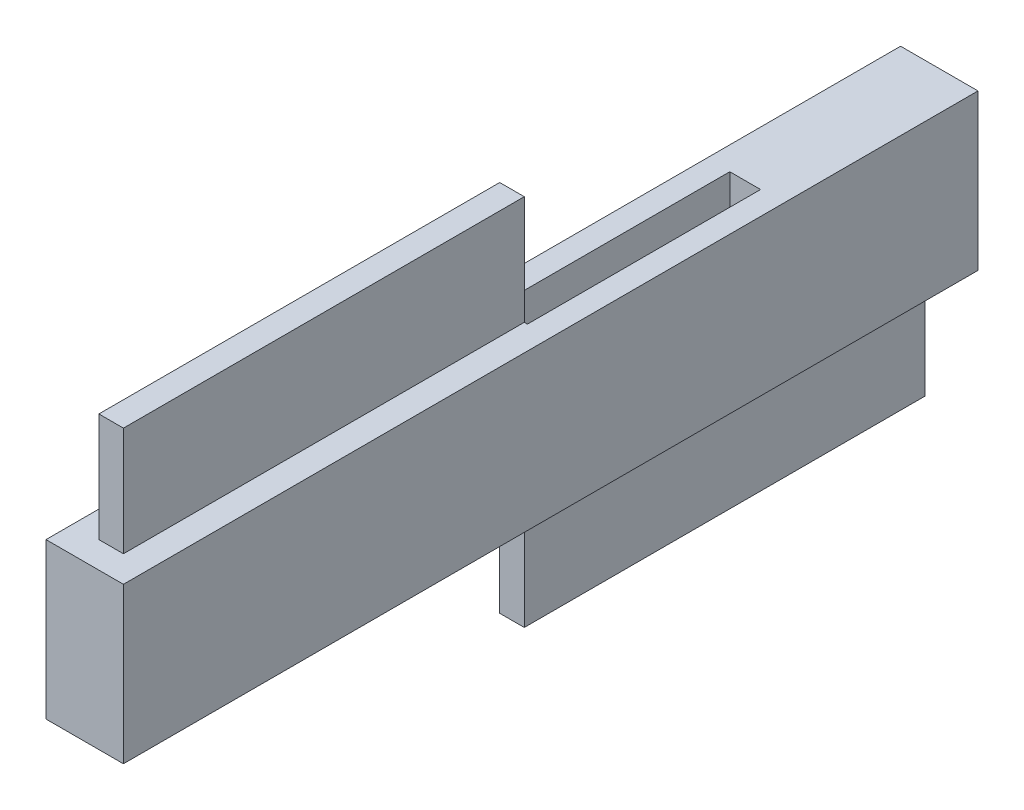
SolidWorks part; units mm, degrees
ref_plane "Front Plane" through (0, 0, 0) normal (0, 0, 1) x (1, 0, 0)
ref_plane "Top Plane" through (0, 0, 0) normal (0, 1, 0) x (1, 0, 0)
ref_plane "Right Plane" through (0, 0, 0) normal (1, 0, 0) x (0, 0, -1)
sketch "Sketch1" plane through (0, 0, 0) normal (0, 1, 0) x (1, 0, 0)
  line L0 (-14.2964, 30.5297) -> (-9.3157, 30.5297)
  line L1 (-9.3157, 30.5297) -> (-9.3157, -24.4422)
  line L2 (-9.3157, -24.4422) -> (-14.2964, -24.4422)
  line L3 (-14.2964, -24.4422) -> (-14.2964, 30.5297)
extrude "Boss-Extrude1" add sketch "Sketch1" along normal blind 10
sketch "Sketch2" plane through (0, 10, 0) normal (0, 1, 0) x (1, 0, 0)
  line L4 (-12.7964, 3.0437) -> (-10.8157, 3.0437)
  line L5 (-12.7964, 18.0437) -> (-10.8157, 18.0437)
  line L8 (-12.7964, 29.0297) -> (-12.7964, -22.9422)
  line L9 (-12.7964, -22.9422) -> (-10.8157, -22.9422)
  line L10 (-10.8157, -22.9422) -> (-10.8157, 29.0297)
  line L11 (-10.8157, 29.0297) -> (-12.7964, 29.0297)
  line L12 (-12.7964, 18.0437) -> (-12.7964, 3.0437)
  line L14 (-10.8157, 3.0437) -> (-10.8157, 18.0437)
  dimension "D1" = 1.5
extrude "Cut-Extrude2" cut sketch "Sketch2" against normal blind 7
sketch "Sketch4" plane through (0, 0, 0) normal (0, -1, 0) x (1, 0, 0)
  line L4 (-10.8157, -3.0437) -> (-12.7964, -3.0437)
  line L8 (-12.7964, 22.9422) -> (-12.7964, -29.0297)
  line L9 (-12.7964, -29.0297) -> (-10.8157, -29.0297)
  line L10 (-10.8157, -29.0297) -> (-10.8157, 22.9422)
  line L11 (-10.8157, 22.9422) -> (-12.7964, 22.9422)
  line L12 (-12.7964, 22.9422) -> (-12.7964, -3.0437)
  line L14 (-10.8157, -3.0437) -> (-10.8157, 22.9422)
  line L15 (-10.8157, 22.9422) -> (-12.7964, 22.9422)
  dimension "D1" = 1.5
extrude "Cut-Extrude3" cut sketch "Sketch4" against normal blind 7
sketch "Sketch5" plane through (0, 0, 0) normal (0, -1, 0) x (1, 0, 0)
  line L8 (-12.5964, -3.0437) -> (-11.0157, -3.0437)
  line L12 (-12.5964, 22.7422) -> (-12.5964, -28.8297)
  line L13 (-12.5964, -28.8297) -> (-11.0157, -28.8297)
  line L14 (-11.0157, -28.8297) -> (-11.0157, 22.7422)
  line L15 (-11.0157, 22.7422) -> (-12.5964, 22.7422)
  line L16 (-12.5964, -3.0437) -> (-12.5964, -28.8297)
  line L17 (-12.5964, -28.8297) -> (-11.0157, -28.8297)
  line L18 (-11.0157, -28.8297) -> (-11.0157, -3.0437)
  dimension "D1" = 1.7
extrude "Boss-Extrude2" add sketch "Sketch5" along normal blind 7 contours L16 L17 L18 L8
sketch "Sketch6" plane through (0, 10, 0) normal (0, 1, 0) x (1, 0, 0)
  line L4 (-11.0157, 3.0437) -> (-12.5964, 3.0437)
  line L8 (-12.5964, 28.8297) -> (-12.5964, -22.7422)
  line L9 (-12.5964, -22.7422) -> (-11.0157, -22.7422)
  line L10 (-11.0157, -22.7422) -> (-11.0157, 28.8297)
  line L11 (-11.0157, 28.8297) -> (-12.5964, 28.8297)
  line L12 (-12.5964, 3.0437) -> (-12.5964, -22.7422)
  line L13 (-12.5964, -22.7422) -> (-11.0157, -22.7422)
  line L14 (-11.0157, -22.7422) -> (-11.0157, 3.0437)
  dimension "D1" = 1.7
extrude "Boss-Extrude3" add sketch "Sketch6" along normal blind 7 contours L12 L13 L14 L4
